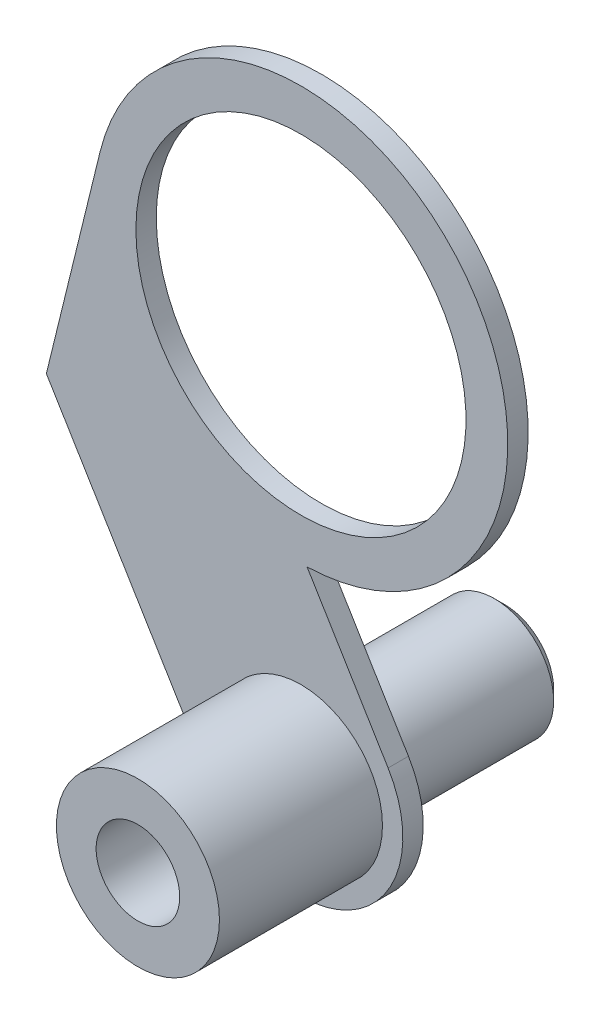
SolidWorks part; units mm, degrees
ref_plane "Спереди" through (0, 0, 0) normal (0, 0, 1) x (1, 0, 0)
ref_plane "Сверху" through (0, 0, 0) normal (0, 1, 0) x (1, 0, 0)
ref_plane "Справа" through (0, 0, 0) normal (1, 0, 0) x (0, 0, -1)
other "Configuration Table"
sketch "Sketch1" plane through (0, 0, 0) normal (1, 0, 0) x (0, 0, -1)
  line L0 (0, 0) -> (18, 0) construction
  line L1 (18, 2.05) -> (18, 2.4)
  line L2 (17.5, 2.9) -> (8, 2.9)
  line L3 (0, 2.05) -> (0, 4)
  line L4 (0, 4) -> (8, 4)
  line L5 (8, 4) -> (8, 2.9)
  line L6 (18, 2.4) -> (17.5, 2.9)
  line L7 (0, 2.05) -> (18, 2.05)
  point P3 (18, 2.9)
revolve "Revolve1" add sketch "Sketch1" angle 360 about L0
sketch "Sketch2" plane through (0, 0, -8) normal (0, 0, -1) x (-1, 0, 0)
  line L3 (9.8578, 21.7117) -> (12.4933, 10.967)
  line L5 (4.276, -2.5915) -> (12.4933, 10.967)
  line L7 (-4.276, 2.5915) -> (-0.3022, 9.1483)
  circle A0 centre (0, 0) radius 2.95
  arc A1 (-4.276, 2.5915) -> (4.276, -2.5915) centre (0, 0) ccw
  circle A2 centre (0, 19.2938) radius 8.1
  arc A3 (9.8578, 21.7117) -> (-0.3022, 9.1483) centre (0, 19.2938) ccw
  dimension "D1" = 45
extrude "Boss-Extrude1" add sketch "Sketch2" along normal blind 1
